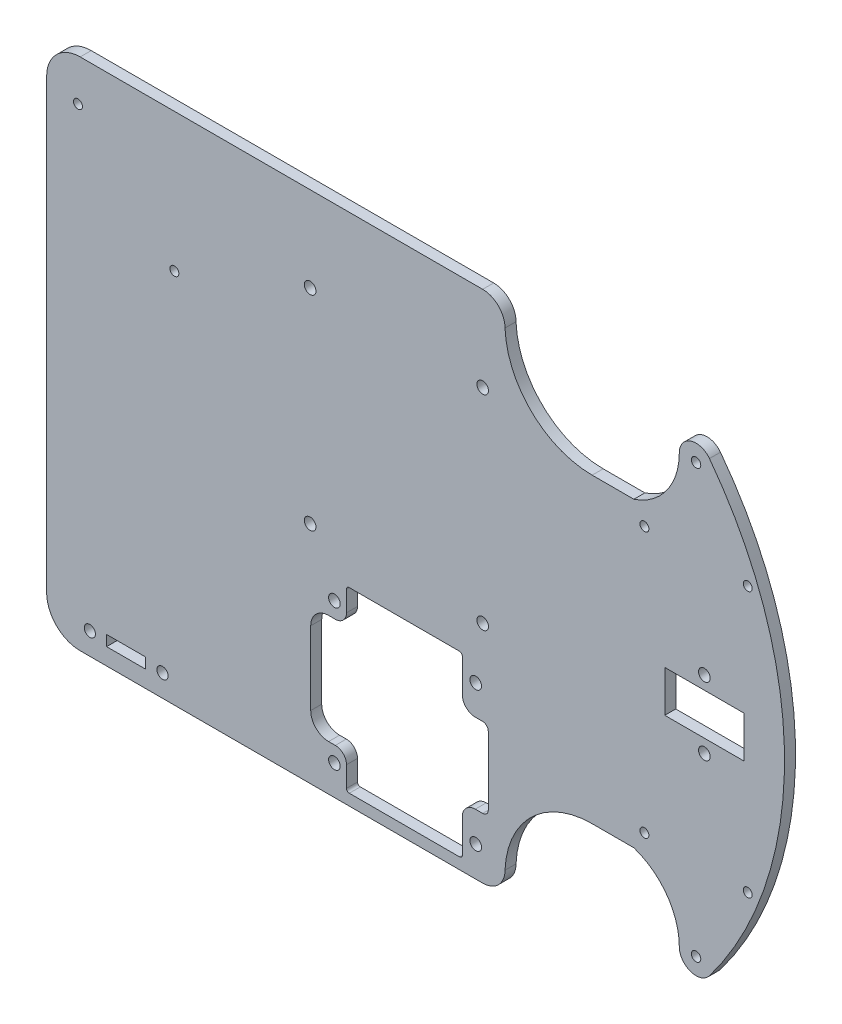
SolidWorks part; units mm, degrees
ref_plane "Alzado" through (0, 0, 0) normal (0, 0, 1) x (1, 0, 0)
ref_plane "Planta" through (0, 0, 0) normal (0, 1, 0) x (1, 0, 0)
ref_plane "Vista lateral" through (0, 0, 0) normal (1, 0, 0) x (0, 0, -1)
sketch "Croquis1" plane through (0, 0, 0) normal (0, 0, 1) x (1, 0, 0)
  line L1 (-104.775, -73.025) -> (104.775, -73.025)
  line L2 (-104.775, -73.025) -> (-104.775, 73.025)
  line L3 (-104.775, 73.025) -> (104.775, 73.025)
  line L4 (104.775, -73.025) -> (104.775, 73.025)
  line L5 (-104.775, -73.025) -> (104.775, 73.025) construction
  line L6 (-104.775, 73.025) -> (104.775, -73.025) construction
  point P0 (0, 0)
  dimension "D1" = 146.05
  dimension "D2" = 209.55
extrude "Saliente-Extruir1" add sketch "Croquis1" along normal blind 3.1242
sketch "Croquis2" plane through (0, 0, 3.1242) normal (0, 0, 1) x (1, 0, 0)
  line L0 (-104.775, -73.025) -> (104.775, -73.025) construction
  line L1 (104.775, 73.025) -> (44.45, 73.025)
  line L2 (104.775, 73.025) -> (104.775, -73.025)
  line L3 (104.775, -73.025) -> (44.45, -73.025)
  line L4 (44.45, 73.025) -> (44.45, -73.025)
  line L5 (0, 0) -> (104.775, 0) construction
  line L6 (70.2056, 73.025) -> (79.0194, 73.025)
  line L7 (70.2056, 73.025) -> (70.2056, 55.6514)
  line L8 (70.2056, 55.6514) -> (79.0194, 55.6514)
  line L9 (79.0194, 73.025) -> (79.0194, 55.6514)
  line L10 (79.0194, -73.025) -> (79.0194, -55.6514)
  line L11 (70.2056, -55.6514) -> (79.0194, -55.6514)
  line L12 (70.2056, -73.025) -> (70.2056, -55.6514)
  line L13 (70.2056, -73.025) -> (79.0194, -73.025)
  circle A0 centre (79.6544, 60.7314) radius 2.921
  circle A1 centre (79.6544, 60.7314) radius 1.3335
  circle A2 centre (79.6544, -60.7314) radius 1.3335
  circle A3 centre (79.6544, -60.7314) radius 2.921
  point P11 (74.6125, 73.025)
  point P12 (74.6125, 55.6514)
  point P13 (79.6544, 57.8104)
  point P14 (82.5754, 60.7314)
  point P28 (82.5754, -60.7314)
  point P29 (79.6544, -57.8104)
  point P30 (74.6125, -55.6514)
  point P31 (74.6125, -73.025)
  point P32 (79.6544, -59.3979)
  point P33 (79.6544, 59.3979)
  point P34 (79.6544, -62.0649)
  point P35 (79.6544, 62.0649)
  dimension "D3" = 5.842
  dimension "D4" = 1.5875
  dimension "D1" = 60.325
  dimension "D2" = 8.8138
  dimension "D5" = 3.556
  dimension "D6" = 17.3736
  dimension "D7" = 118.7958
  dimension "D8" = 118.7958
  dimension "D9" = 124.1298
extrude "Cortar-Extruir1" cut sketch "Croquis2" against normal through all contours L9 A1 | L9 A1 | A2
sketch "Croquis9" plane through (0, 0, 3.1242) normal (0, 0, 1) x (1, 0, 0)
  line L0 (64.9859, 37.6809) -> (94.3229, 37.6809) construction
  line L1 (0, 0) -> (104.775, 0) construction
  line L2 (104.775, -73.025) -> (104.775, 73.025) construction
  line L3 (64.9859, -37.6809) -> (94.3229, -37.6809) construction
  circle A0 centre (64.9859, 37.6809) radius 1.27
  circle A1 centre (94.3229, 37.6809) radius 1.27
  circle A2 centre (94.3229, 37.6809) radius 2.794
  circle A3 centre (79.6544, 60.7314) radius 1.3335 construction
  circle A4 centre (79.6544, 60.7314) radius 1.3335
  circle A5 centre (94.3229, -37.6809) radius 1.27
  circle A6 centre (64.9859, -37.6809) radius 1.27
  point P4 (79.6544, 62.0649)
  point P5 (94.3229, 34.8869)
  point P9 (79.6544, 37.6809)
  point P22 (94.3229, -34.8869)
  dimension "D1" = 29.337
  dimension "D2" = 2.54
  dimension "D3" = 27.178
  dimension "D4" = 5.588
extrude "Cortar-Extruir6" cut sketch "Croquis9" against normal through all
sketch "Croquis3" plane through (0, 0, 3.1242) normal (0, 0, 1) x (1, 0, 0)
  line L0 (104.775, -73.025) -> (104.775, 73.025) construction
  line L1 (104.775, 73.025) -> (-104.775, 73.025) construction
  line L2 (0, 0) -> (104.775, 0) construction
  line L3 (25.4, 73.025) -> (74.8919, 73.025)
  line L4 (25.4, 73.025) -> (25.4, 42.8625)
  line L5 (25.4, 42.8625) -> (74.8919, 42.8625)
  line L6 (74.8919, 73.025) -> (74.8919, 42.8625)
  line L7 (74.8919, -73.025) -> (74.8919, -42.8625)
  line L8 (25.4, -42.8625) -> (74.8919, -42.8625)
  line L9 (25.4, -73.025) -> (25.4, -42.8625)
  line L10 (25.4, -73.025) -> (74.8919, -73.025)
  line L11 (-104.775, -73.025) -> (104.775, -73.025) construction
  line L12 (-95.25, 73.025) -> (0, 73.025)
  line L13 (-104.775, 63.5) -> (-104.775, -63.5)
  line L14 (-95.25, -73.025) -> (0, -73.025)
  line L15 (0, 73.025) -> (0, -73.025)
  circle A0 centre (79.6544, 60.7314) radius 4.7625
  arc A1 (83.4547, 63.6018) -> (83.4547, -63.6018) centre (-0.7522, 0) cw
  arc A2 (50.146, 42.8625) -> (74.8919, 60.7314) centre (56.0674, 60.7314) ccw
  arc A3 (19.05, 73.025) -> (25.4, 66.675) centre (19.05, 66.675) cw
  arc A4 (25.4, 66.675) -> (50.146, 42.8625) centre (50.146, 67.6267) ccw
  arc A5 (25.4, -66.675) -> (50.146, -42.8625) centre (50.146, -67.6267) cw
  arc A6 (19.05, -73.025) -> (25.4, -66.675) centre (19.05, -66.675) ccw
  arc A7 (50.146, -42.8625) -> (74.8919, -60.7314) centre (56.0674, -60.7314) cw
  circle A8 centre (79.6544, -60.7314) radius 4.7625
  arc A9 (-104.775, -63.5) -> (-95.25, -73.025) centre (-95.25, -63.5) ccw
  arc A10 (-95.25, 73.025) -> (-104.775, 63.5) centre (-95.25, 63.5) ccw
  point P48 (-104.775, 73.025)
  dimension "D1" = 30.1625
  dimension "D3" = 6.35
  dimension "D4" = 9.525
  dimension "D5" = 9.525
  dimension "D2" = 25.4
extrude "Cortar-Extruir2" cut sketch "Croquis3" against normal through all
sketch "Croquis5" plane through (0, 0, 3.1242) normal (0, 0, 1) x (1, 0, 0)
  line L0 (-95.25, -73.025) -> (19.05, -73.025) construction
  line L1 (-29.7815, -19.2786) -> (20.6375, -19.2786)
  line L2 (-29.7815, -19.2786) -> (-29.7815, -69.85)
  line L3 (-29.7815, -69.85) -> (20.6375, -69.85)
  line L4 (20.6375, -19.2786) -> (20.6375, -69.85)
  line L5 (-29.7815, -44.5643) -> (20.6375, -44.5643) construction
  line L6 (25.4, -63.5) -> (25.4, -62.2144) construction
  line L7 (20.6375, -69.85) -> (13.2715, -69.85)
  line L8 (20.6375, -69.85) -> (20.6375, -19.2786)
  line L9 (20.6375, -19.2786) -> (13.2715, -19.2786)
  line L10 (13.2715, -69.85) -> (13.2715, -19.2786)
  line L11 (-29.7815, -19.2786) -> (-19.6215, -19.2786)
  line L12 (-29.7815, -19.2786) -> (-29.7815, -69.85)
  line L13 (-29.7815, -69.85) -> (-19.6215, -69.85)
  line L14 (-19.6215, -19.2786) -> (-19.6215, -69.85)
  line L15 (13.2715, -33.2486) -> (20.6375, -33.2486)
  line L16 (13.2715, -33.2486) -> (13.2715, -55.88)
  line L17 (13.2715, -55.88) -> (20.6375, -55.88)
  line L18 (20.6375, -33.2486) -> (20.6375, -55.88)
  line L19 (-19.6215, -29.0576) -> (-29.7815, -29.0576)
  line L20 (-19.6215, -29.0576) -> (-19.6215, -60.071)
  line L21 (-19.6215, -60.071) -> (-29.7815, -60.071)
  line L22 (-29.7815, -29.0576) -> (-29.7815, -60.071)
  circle A0 centre (17.0815, -24.7396) radius 1.651
  circle A1 centre (-23.0505, -24.6126) radius 1.651
  circle A2 centre (17.0815, -64.389) radius 1.651
  circle A3 centre (-23.0505, -64.516) radius 1.651
  arc A4 (19.05, -55.88) -> (20.6375, -54.2925) centre (19.05, -54.2925) ccw
  arc A5 (16.9545, -55.88) -> (13.2715, -59.563) centre (16.9545, -59.563) ccw
  arc A6 (-24.7015, -60.071) -> (-29.7815, -54.991) centre (-24.7015, -54.991) cw
  arc A7 (-22.7965, -60.071) -> (-19.6215, -63.246) centre (-22.7965, -63.246) cw
  arc A8 (19.05, -33.2486) -> (20.6375, -34.8361) centre (19.05, -34.8361) cw
  arc A9 (16.9545, -33.2486) -> (13.2715, -29.5656) centre (16.9545, -29.5656) cw
  arc A10 (-24.7015, -29.0576) -> (-29.7815, -34.1376) centre (-24.7015, -34.1376) ccw
  arc A11 (-22.7965, -29.0576) -> (-19.6215, -25.8826) centre (-22.7965, -25.8826) ccw
  arc A12 (-19.6215, -20.0724) -> (-18.8278, -19.2786) centre (-18.8278, -20.0724) cw
  arc A13 (12.4777, -19.2786) -> (13.2715, -20.0724) centre (12.4777, -20.0724) cw
  arc A14 (12.4777, -69.85) -> (13.2715, -69.0563) centre (12.4777, -69.0563) ccw
  arc A15 (-19.6215, -69.0563) -> (-18.8278, -69.85) centre (-18.8278, -69.0563) ccw
  point P4 (18.7325, -24.7396)
  point P5 (17.0815, -23.0886)
  point P6 (-23.0505, -22.9616)
  point P14 (-24.7015, -24.6126)
  dimension "D5" = 3.302
  dimension "D16" = 1.5875
  dimension "D17" = 3.175
  dimension "D18" = 0.7937
  dimension "D1" = 50.5714
  dimension "D2" = 50.419
  dimension "D3" = 3.81
  dimension "D4" = 1.905
  dimension "D6" = 3.175
  dimension "D7" = 4.7625
  dimension "D8" = 5.08
  dimension "D9" = 3.683
  dimension "D10" = 7.366
  dimension "D11" = 10.16
  dimension "D12" = 13.97
  dimension "D13" = 13.97
  dimension "D14" = 9.779
  dimension "D15" = 9.779
extrude "Driver" cut sketch "Croquis5" against normal through all contours L22 L5 L14 L19 A10 | L5 L12 A6 L21 L20 | L14 L5 L16 L10 L1 | L16 L5 L18 A8 L15 | L5 L10 L17 A4 L8 | L5 L20 L14 L3 L10 | A5 L17 L10 | L21 A7 L14 | A11 L19 L14 | L15 A9 L10 | A1 | A3 | A2 | A0
sketch "Croquis6" plane through (0, 0, 3.1242) normal (0, 0, 1) x (1, 0, 0)
  line L0 (-33.45, 19.8814) -> (22.55, 19.8814)
  line L1 (-29.95, 48.8814) -> (19.05, 48.8814)
  line L2 (-29.95, 48.8814) -> (-29.95, -9.1186)
  line L3 (-29.95, -9.1186) -> (19.05, -9.1186)
  line L4 (19.05, 48.8814) -> (19.05, -9.1186)
  line L5 (-18.8278, -19.2786) -> (12.4777, -19.2786) construction
  line L6 (-5.45, -9.1186) -> (-5.45, 74.7014)
  circle A0 centre (-29.95, 48.8814) radius 1.651
  circle A1 centre (19.05, 48.8814) radius 1.651
  circle A2 centre (19.05, -9.1186) radius 1.651
  circle A3 centre (-29.95, -9.1186) radius 1.651
  point P13 (-5.45, 19.8814)
  point P14 (19.05, 19.8814)
  point P16 (-5.45, 48.8814)
  dimension "D1" = 3.302
  dimension "D2" = 58
  dimension "D3" = 49
  dimension "D4" = 56
  dimension "D5" = 6.35
  dimension "D6" = 10.16
  dimension "D7" = 83.82
extrude "RasPi" cut sketch "Croquis6" against normal through all contours A3 | A2 | A1 | A0
sketch "Croquis8" plane through (0, 0, 3.1242) normal (0, 0, 1) x (1, 0, 0)
  line L0 (-95.885, 61.138) -> (-68.4952, 33.7483)
  line L2 (-67.2252, 62.657) -> (-88.8152, 62.657)
  line L3 (-95.885, 61.138) -> (-68.4952, 61.138)
  line L4 (-95.885, 61.138) -> (-95.885, 33.7483)
  line L5 (-95.885, 33.7483) -> (-68.4952, 33.7483)
  line L6 (-68.4952, 61.138) -> (-68.4952, 33.7483)
  line L7 (-104.775, 63.5) -> (-104.775, -63.5) construction
  line L8 (-67.2252, 62.657) -> (-67.2252, 37.5043)
  line L9 (-67.2252, 37.5043) -> (-88.8152, 37.5043)
  line L10 (-88.8152, 62.657) -> (-88.8152, 37.5043)
  circle A0 centre (-95.885, 61.138) radius 1.27
  circle A1 centre (-68.4952, 33.7483) radius 1.27
  point P12 (-67.2252, 33.7483)
  point P13 (0, 0)
  dimension "D1" = 8.89
  dimension "D3" = 2.54
  dimension "D4" = 2.54
  dimension "D2" = 38.735
  dimension "D5" = 21.59
extrude "Cortar-Extruir5" cut sketch "Croquis8" against normal through all contours A0 | A1
sketch "Croquis7" plane through (0, 0, 3.1242) normal (0, 0, 1) x (1, 0, 0)
  line L0 (-82.1901, 33.7483) -> (-82.1901, -65.2653) construction
  line L1 (-87.7464, -65.2653) -> (-76.6339, -65.2653)
  line L2 (-87.7464, -65.2653) -> (-87.7464, -68.2625)
  line L3 (-87.7464, -68.2625) -> (-76.6339, -68.2625)
  line L4 (-76.6339, -65.2653) -> (-76.6339, -68.2625)
  line L5 (-95.885, 61.138) -> (-68.4952, 61.138)
  line L6 (-95.885, 61.138) -> (-95.885, 33.7483)
  line L7 (-95.885, 33.7483) -> (-68.4952, 33.7483)
  line L8 (-68.4952, 61.138) -> (-68.4952, 33.7483)
  line L9 (-95.25, -73.025) -> (19.05, -73.025) construction
  circle A0 centre (-71.8714, -66.7639) radius 1.5875
  circle A1 centre (-92.5089, -66.7639) radius 1.5875
  point P16 (-76.6339, -66.7639)
  point P17 (0, 0)
  point P20 (-87.7464, -66.7639)
  dimension "D4" = 3.175
  dimension "D1" = 2.9972
  dimension "D2" = 11.1125
  dimension "D3" = 4.7625
  dimension "D5" = 4.7625
extrude "Cortar-Extruir7" cut sketch "Croquis7" against normal through all contours A1 | A0 | L3 L4 L1 L2
sketch "Croquis10" plane through (0, 0, 3.1242) normal (0, 0, 1) x (1, 0, 0)
  line L0 (-104.775, 63.5) -> (-104.775, -63.5) construction
  line L1 (61.3912, -19.4466) -> (54.8894, -19.4466)
  line L2 (61.3912, -19.4466) -> (61.3912, 12.2487)
  line L3 (61.3912, 12.2487) -> (54.8894, 12.2487)
  line L4 (54.8894, -19.4466) -> (54.8894, 12.2487)
  line L5 (61.3912, -19.4466) -> (54.8894, 12.2487) construction
  line L6 (61.3912, 12.2487) -> (54.8894, -19.4466) construction
  line L7 (82.0039, 9.652) -> (82.0039, -9.652) construction
  line L8 (70.7644, -5.8928) -> (93.2434, -5.8928)
  line L9 (70.7644, -5.8928) -> (70.7644, 5.8928)
  line L10 (70.7644, 5.8928) -> (93.2434, 5.8928)
  line L11 (93.2434, -5.8928) -> (93.2434, 5.8928)
  line L12 (70.7644, -5.8928) -> (93.2434, 5.8928) construction
  line L13 (70.7644, 5.8928) -> (93.2434, -5.8928) construction
  line L14 (93.2434, -5.8928) -> (93.2434, 5.8928)
  line L15 (93.2434, 3.1134) -> (93.2434, -1.9666)
  line L16 (82.0039, 9.652) -> (82.0039, -17.272) construction
  circle A0 centre (82.0039, 9.652) radius 1.651
  circle A1 centre (82.0039, -9.652) radius 1.651
  circle A2 centre (82.0039, 9.652) radius 1.651
  point P0 (58.1403, -3.599)
  point P7 (54.8898, -19.4306)
  point P16 (82.0039, 0)
  point P21 (93.2434, 0)
  point P22 (0, 0)
  dimension "D5" = 3.302
  dimension "D1" = 159.6644
  dimension "D2" = 19.304
  dimension "D3" = 22.479
  dimension "D4" = 11.7856
  dimension "D6" = 26.924
  dimension "D7" = 175.5394
extrude "Cortar-Extruir10" cut sketch "Croquis10" against normal through all contours A0 | L8 L11 L14 L10 L9 | A1
